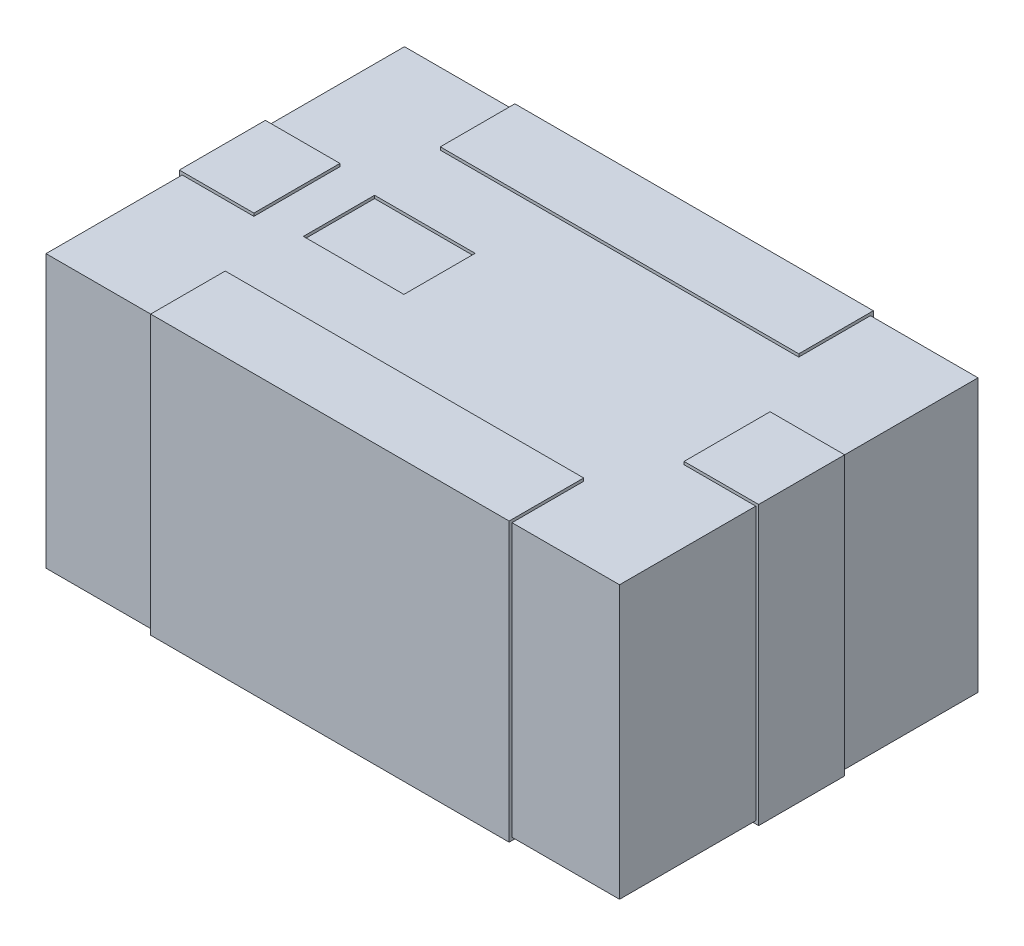
SolidWorks part; units mm, degrees
ref_plane "Front Plane" through (0, 0, 0) normal (0, 0, 1) x (1, 0, 0)
ref_plane "Top Plane" through (0, 0, 0) normal (0, 1, 0) x (1, 0, 0)
ref_plane "Right Plane" through (0, 0, 0) normal (1, 0, 0) x (0, 0, -1)
sketch "Sketch1" plane through (0, 0, 0) normal (0, 1, 0) x (1, 0, 0)
  line L1 (-1, 0.625) -> (1, 0.625)
  line L2 (-1, 0.625) -> (-1, -0.625)
  line L3 (-1, -0.625) -> (1, -0.625)
  line L4 (1, 0.625) -> (1, -0.625)
  line L5 (-1, 0.625) -> (1, -0.625) construction
  line L6 (-1, -0.625) -> (1, 0.625) construction
  point P0 (0, 0)
  dimension "D1" = 1.25
  dimension "D2" = 2
extrude "Boss-Extrude1" add sketch "Sketch1" along normal mid plane 0.95
sketch "Sketch2" plane through (0, 0, 0) normal (0, 1, 0) x (1, 0, 0)
  line L0 (0, 0) -> (-1.1727, 0) construction
  line L1 (-1.01, 0.15) -> (-0.75, 0.15)
  line L2 (-1.01, 0.15) -> (-1.01, -0.15)
  line L3 (-1.01, -0.15) -> (-0.75, -0.15)
  line L4 (-0.75, 0.15) -> (-0.75, -0.15)
  line L5 (-0.625, 0.635) -> (0.625, 0.635)
  line L6 (-0.625, 0.635) -> (-0.625, 0.375)
  line L7 (-0.625, 0.375) -> (0.625, 0.375)
  line L8 (0.625, 0.635) -> (0.625, 0.375)
  line L9 (0, 0) -> (0, 0.8561) construction
  line L10 (-1, 0.625) -> (-1, -0.625) construction
  line L11 (1, 0.625) -> (-1, 0.625) construction
  line L12 (0.625, -0.635) -> (0.625, -0.375)
  line L13 (-0.625, -0.375) -> (0.625, -0.375)
  line L14 (-0.625, -0.635) -> (-0.625, -0.375)
  line L15 (-0.625, -0.635) -> (0.625, -0.635)
  line L16 (0.75, 0.15) -> (0.75, -0.15)
  line L17 (1.01, -0.15) -> (0.75, -0.15)
  line L18 (1.01, 0.15) -> (1.01, -0.15)
  line L19 (1.01, 0.15) -> (0.75, 0.15)
  point P11 (0, 0)
  point P13 (0, 0)
  dimension "D1" = 0.3
  dimension "D2" = 0.01
  dimension "D3" = 0.01
  dimension "D4" = 1.25
  dimension "D5" = 0.25
  dimension "D6" = 0.25
extrude "Boss-Extrude2" add sketch "Sketch2" along normal mid plane 0.97
sketch "Sketch3" plane through (0, 0.475, 0) normal (0, 1, 0) x (1, 0, 0)
  line L1 (-0.6034, 0.1242) -> (-0.2527, 0.1242)
  line L2 (-0.6034, 0.1242) -> (-0.6034, -0.1242)
  line L3 (-0.6034, -0.1242) -> (-0.2527, -0.1242)
  line L4 (-0.2527, 0.1242) -> (-0.2527, -0.1242)
  line L5 (-0.6034, 0.1242) -> (-0.2527, -0.1242) construction
  line L6 (-0.6034, -0.1242) -> (-0.2527, 0.1242) construction
  point P0 (-0.428, 0)
  point P5 (-0.428, 0)
extrude "Cut-Extrude1" cut sketch "Sketch3" against normal blind 0.01
